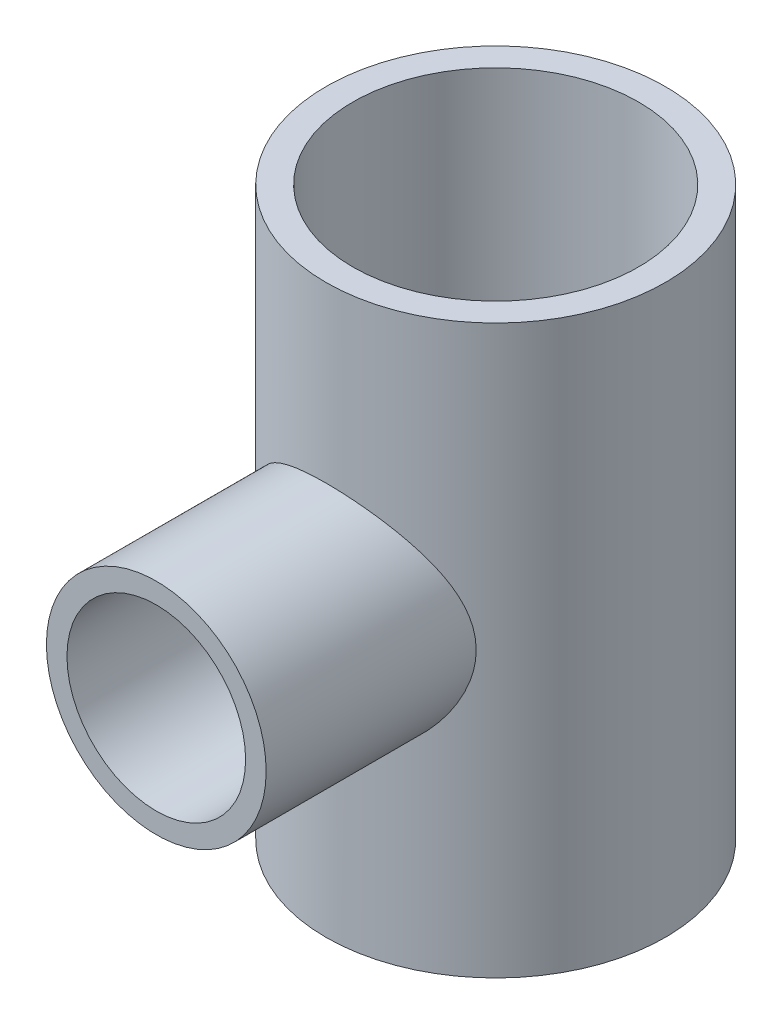
SolidWorks part; units mm, degrees
ref_plane "前视基准面" through (0, 0, 0) normal (0, 0, 1) x (1, 0, 0)
ref_plane "上视基准面" through (0, 0, 0) normal (0, 1, 0) x (1, 0, 0)
ref_plane "右视基准面" through (0, 0, 0) normal (1, 0, 0) x (0, 0, -1)
sketch "草图1" plane through (0, 0, 0) normal (0, 1, 0) x (1, 0, 0)
  circle A0 centre (0, 0) radius 19
  circle A1 centre (0, 0) radius 16
  dimension "D1" = 38
  dimension "D2" = 32
extrude "凸台-拉伸1" add sketch "草图1" along normal blind 63.5 contours A0 | A1
sketch "草图2" plane through (0, 0, 0) normal (0, 0, 1) x (1, 0, 0)
  line L0 (0, 63.5) -> (0, 0) construction
  line L1 (16, 63.5) -> (-16, 63.5) construction
  circle A0 centre (0, 31.75) radius 10
  circle A1 centre (0, 31.75) radius 12.3
extrude "凸台-拉伸2" add sketch "草图2" along normal blind 38 contours A1 | A0
sketch "草图3" plane through (0, 0, 0) normal (0, -1, 0) x (1, 0, 0)
  circle A0 centre (0, 0) radius 16
extrude "切除-拉伸1" cut sketch "草图3" against normal through all
sketch "草图7" plane through (0, 0, 38) normal (0, 0, 1) x (1, 0, 0)
  circle A0 centre (0, 31.75) radius 10
extrude "切除-拉伸2" cut sketch "草图7" against normal up to next
